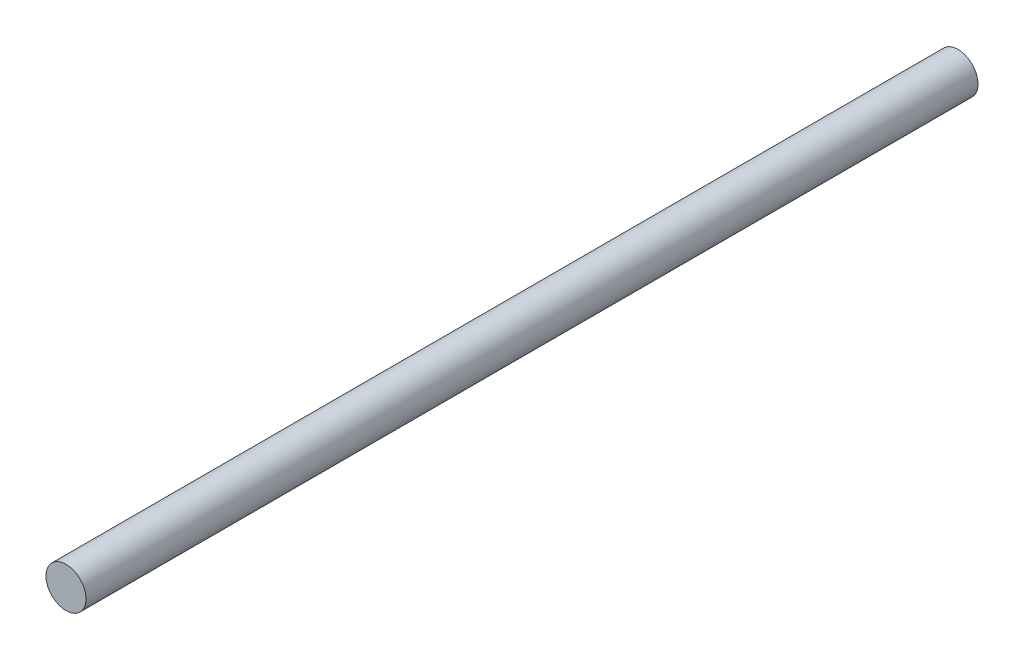
SolidWorks part; units mm, degrees
ref_plane "Front Plane" through (0, 0, 0) normal (0, 0, 1) x (1, 0, 0)
ref_plane "Top Plane" through (0, 0, 0) normal (0, 1, 0) x (1, 0, 0)
ref_plane "Right Plane" through (0, 0, 0) normal (1, 0, 0) x (0, 0, -1)
sketch "Sketch1" plane through (0, 0, 0) normal (0, 0, 1) x (1, 0, 0)
  circle A0 centre (0, 0) radius 10
  dimension "D1" = 20
extrude "Boss-Extrude1" add sketch "Sketch1" along normal mid plane 445
